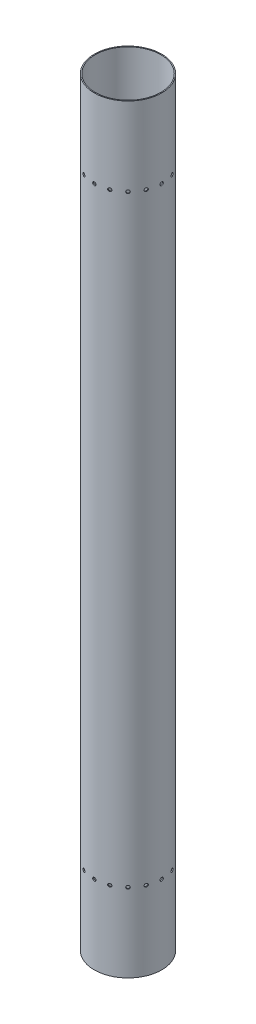
SolidWorks part; units mm, degrees
ref_plane "Front Plane" through (0, 0, 0) normal (0, 0, 1) x (1, 0, 0)
ref_plane "Top Plane" through (0, 0, 0) normal (0, 1, 0) x (1, 0, 0)
ref_plane "Right Plane" through (0, 0, 0) normal (1, 0, 0) x (0, 0, -1)
sketch "Sketch1" plane through (0, 0, 0) normal (0, 1, 0) x (1, 0, 0)
  circle A0 centre (0, 0) radius 63.5
  circle A1 centre (0, 0) radius 65.405
  dimension "D1" = 127
  dimension "D2" = 130.81
extrude "Boss-Extrude1" add sketch "Sketch1" against normal blind 1473.2
ref_plane "Plane1" through (0, 0, 65.405) normal (0, 0, 1) x (1, 0, 0)
ref_axis "Axis1" through (0, -1473.2, 0) along (0, 1, 0)
sketch "Sketch2" plane through (0, 0, 65.405) normal (0, 0, 1) x (1, 0, 0)
  line L0 (-65.405, -1473.2) -> (65.405, -1473.2) construction
  circle A0 centre (0, -1320.8) radius 3.175
  dimension "D1" = 6.35
  dimension "D2" = 152.4
extrude "Engine Attachment Holes" cut sketch "Sketch2" against normal up to next contours A0
pattern_circular "CirPattern1" count 16 over 360 about axis through (0, -1473.2, 0) along (0, 1, 0) of "Engine Attachment Holes"
sketch "Sketch3" plane through (0, 0, 65.405) normal (0, 0, 1) x (1, 0, 0)
  line L0 (65.405, 0) -> (-65.405, 0) construction
  circle A0 centre (0, -152.4) radius 3.175
  point P4 (0, 0)
  dimension "D1" = 6.35
  dimension "D2" = 152.4
extrude "Recovery Plate Holes" cut sketch "Sketch3" against normal up to next
pattern_circular "CirPattern2" count 16 over 360 about axis through (0, 0, 0) along (0, 1, 0) of "Recovery Plate Holes"
